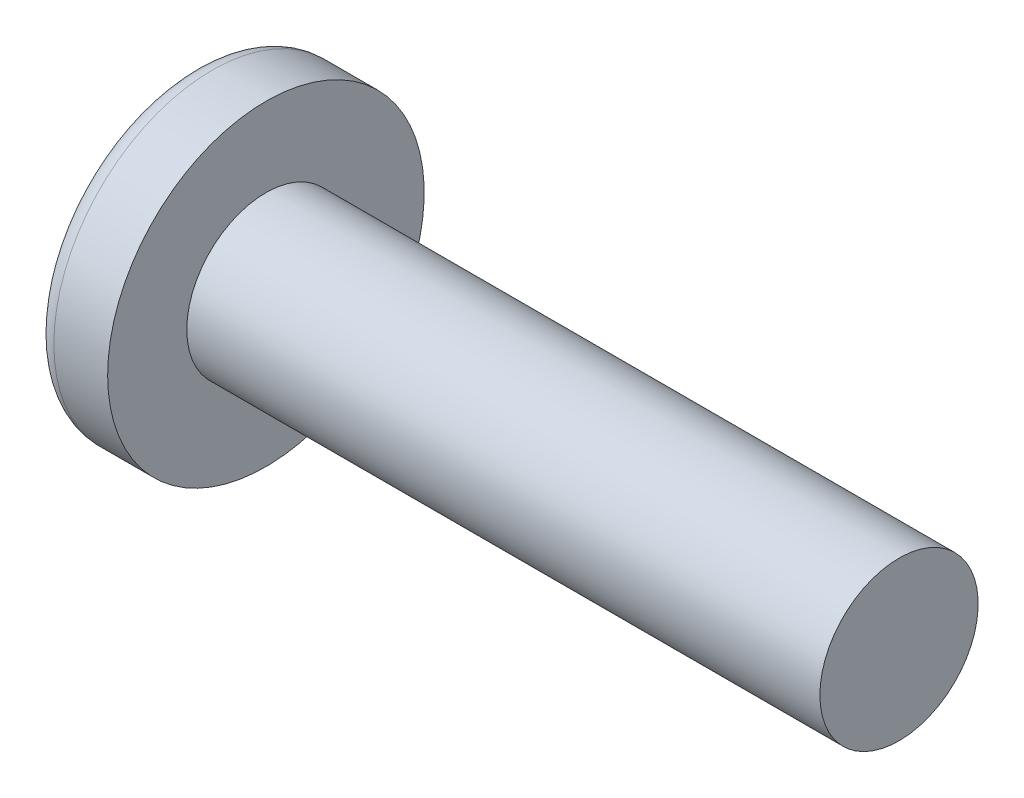
SolidWorks part; units mm, degrees
ref_plane "Plane1" through (0, 0, 0) normal (0, 0, 1) x (1, 0, 0)
ref_plane "Plane2" through (0, 0, 0) normal (0, 1, 0) x (1, 0, 0)
ref_plane "Plane3" through (0, 0, 0) normal (1, 0, 0) x (0, 0, -1)
sketch "BodySke" plane through (0, 0, 0) normal (0, 0, 1) x (1, 0, 0)
  line L0 (7.5, 5) -> (7.5, 10)
  line L1 (9, 6.35) -> (9, -3.175) construction
  line L2 (-25.4, 0) -> (127, 0) construction
  line L3 (47.5, 0) -> (0, 0)
  line L4 (7.5, 5) -> (47.5, 5)
  line L5 (47.5, 5) -> (47.5, 0)
  line L6 (4.1004, 10) -> (7.5, 10)
  line L7 (7.5, -5) -> (47.5, -5) construction
  line L8 (7.5, 6.35) -> (7.5, -3.175) construction
  arc A0 (3.1356, 9.5135) -> (0, 0) centre (16, 0) ccw
  arc A2 (3.1356, 9.5135) -> (4.1004, 10) centre (4.1004, 8.8) cw
revolve "Base-Revolve" add sketch "BodySke" angle 360 about L2
cosmetic thread "ThreadCosmetic" [suppressed] parameters "Thread_length"=4.5, "Thread_minor"=8.344
sketch "Sketch3" plane through (0, 0, 0) normal (1, 0, 0) x (0, 0, -1)
  line L0 (0.92, -5.09) -> (-0.92, -5.09)
  line L1 (0.92, -5.09) -> (0.92, 5.09)
  line L2 (-0.92, 5.09) -> (0.92, 5.09)
  line L3 (-0.92, 5.09) -> (-0.92, -5.09)
  dimension "D1" = 1.45
  dimension "D2" = 0.37
ref_plane "Plane4" through (6.09, 0, 0) normal (1, 0, 0) x (0, 0, -1)
sketch "Sketch4" plane through (6.09, 0, 0) normal (1, 0, 0) x (0, 0, -1)
  line L0 (0.46, -0.46) -> (-0.46, -0.46)
  line L1 (0.46, -0.46) -> (0.46, 0.46)
  line L2 (-0.46, 0.46) -> (0.46, 0.46)
  line L3 (-0.46, 0.46) -> (-0.46, -0.46)
  dimension "D2" = 0.37
  dimension "D1" = 0.37
  dimension "D3" = 0.185
  dimension "D4" = 0.185
loft "Cut-Loft1" cut profiles "Sketch3", "Sketch4"
pattern_circular "CirPattern1" count 2 every 90 about axis through (0, 0, 0) along (1, 0, 0) of "Cut-Loft1"
sketch "ThdSchSke" plane through (0, 0, 0) normal (0, 0, 1) x (1, 0, 0)
  line L0 (9, -4.172) -> (8.4202, -5)
  line L1 (9, -4.172) -> (9.5798, -5)
  line L2 (9.5798, -5) -> (9.5798, -6.25)
  line L3 (-3.175, 0) -> (5.1513, 0) construction
  line L5 (9.5798, -6.25) -> (8.4202, -6.25)
  line L6 (8.4202, -6.25) -> (8.4202, -5)
  dimension "SideAngle" = 55
  dimension "VeeAngle" = 70
  dimension "Thread_minor" = 2.439
  dimension "Overcut" = 3.75
  dimension "Diameter" = 3
  dimension "Start" = 2.9
revolve "ThreadSchematic" [suppressed] cut sketch "ThdSchSke" angle 360 about L3
pattern_linear "ThdSchPat" [suppressed]
equation "\"D1@Sketch3\" = \"Cross_dia@Sketch3\" / 2"
equation "\"D2@Sketch3\" = \"Cross_width@Sketch3\" / 2"
equation "\"D1@Sketch4\" = \"Cross_width@Sketch3\" *.5"
equation "\"D2@Sketch4\" = \"D1@Sketch4\""
equation "\"D3@Sketch4\" = \"D1@Sketch4\" / 2"
equation "\"D4@Sketch4\" = \"D2@Sketch4\" / 2"
equation "\"Thread_length@ThreadCosmetic\" = ((sgn( (\"Length@BodySke\" - \"Advance@BodySke\" ) - \"Thread_nom@BodySke\" )-1)*( (\"Length@BodySke\" - \"Advance@BodySke\" ) - \"Thread_nom@BodySke\" ))/-2+ \"Thread_nom@BodySke\""
equation "\"Thread_minor@ThdSchSke\" = \"Thread_minor@ThreadCosmetic\""
equation "\"Diameter@ThdSchSke\" = \"Diameter@BodySke\""
equation "\"Overcut@ThdSchSke\" = \"Diameter@BodySke\" * 1.25"
equation "\"Start@ThdSchSke\" = \"Head_ht@BodySke\" + \"Length@BodySke\" - \"Thread_length@ThreadCosmetic\"  '---Non-countersunk---"
equation "\"Num_threads@ThdSchPat\" = int( \"Thread_length@ThreadCosmetic\" / \"Advance@BodySke\" + 0.999 )  + 1"
equation "\"Advance@ThdSchPat\" = \"Thread_length@ThreadCosmetic\" /  (\"Num_threads@ThdSchPat\" - 1) 'relax it"
